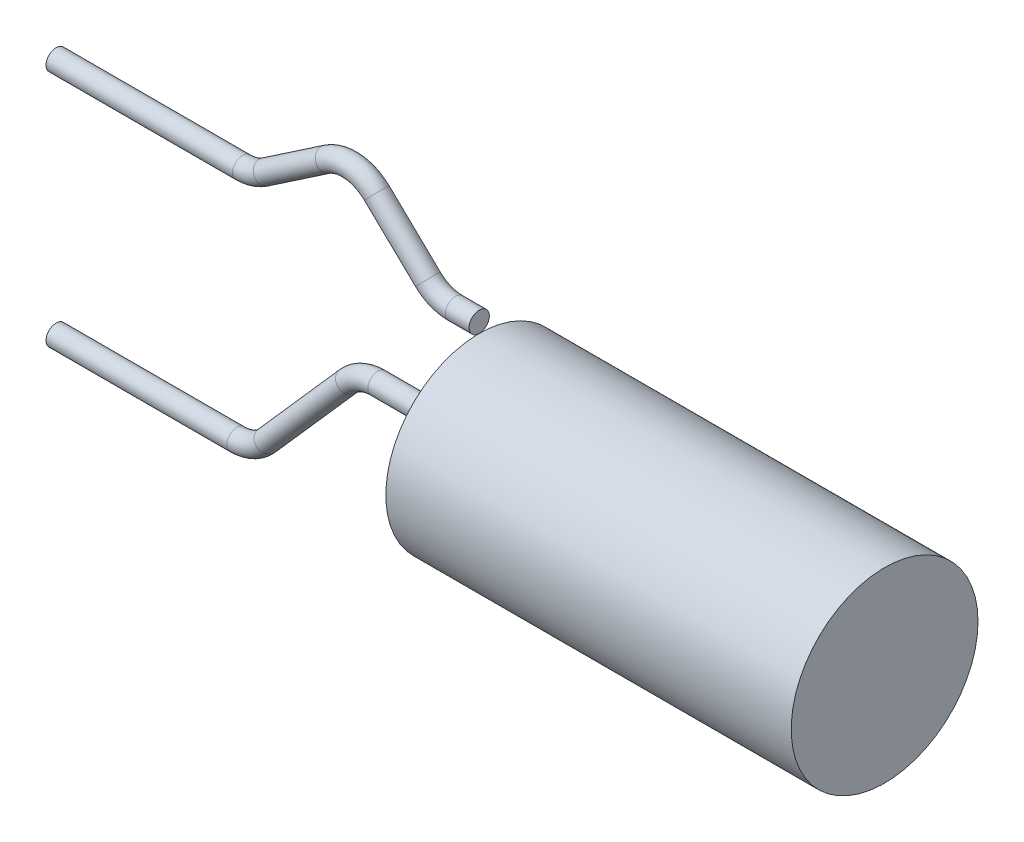
SolidWorks part; units mm, degrees
ref_plane "Plane1" through (0, 0, 0) normal (0, 0, 1) x (1, 0, 0)
ref_plane "Plane2" through (0, 0, 0) normal (0, 1, 0) x (1, 0, 0)
ref_plane "Plane3" through (0, 0, 0) normal (1, 0, 0) x (0, 0, -1)
sketch "Sketch1" plane through (0, 0, 0) normal (0, 0, 1) x (1, 0, 0)
  line L0 (0, 0) -> (-25.9084, 0) construction
  line L1 (-10.2, 0) -> (0, 0)
  line L2 (0, 0) -> (0, 2.35)
  line L3 (0, 2.35) -> (-10.2, 2.35)
  line L4 (-10.2, 0) -> (-10.2, 2.35)
  dimension "D1" = 10.2
  dimension "D2" = 4.7
revolve "Revolve1" add sketch "Sketch1" angle 360 about L0
sketch "Sketch4" plane through (0, 0, 0) normal (0, 0, 1) x (1, 0, 0)
  line L0 (-10.2, 0) -> (-12.7486, 0)
  line L1 (-10.2, 2.35) -> (-10.2, -2.35) construction
  line L2 (-13.4986, -0.3386) -> (-15.5472, -2.6614)
  line L3 (-16.2972, -3) -> (-20.8458, -3)
  line L5 (-15.8458, 3) -> (-13.3629, 4.6839) construction
  line L6 (-15.8458, 3) -> (-20.8458, 3) construction
  line L7 (0, 0) -> (-30.9014, 0) construction
  line L8 (-13.3629, 4.6839) -> (-11.2, 2.605) construction
  line L9 (0, 2.35) -> (-10.2, 2.35) construction
  line L10 (-11.2, 2.605) -> (-10.2, 2.605) construction
  arc A0 (-15.5472, -2.6614) -> (-16.2972, -3) centre (-16.2972, -2) cw
  arc A1 (-12.7486, 0) -> (-13.4986, -0.3386) centre (-12.7486, -1) ccw
  point P17 (-15.8458, -3)
  point P20 (-13.2, 0)
  dimension "D9" = 1
  dimension "D1" = 3
  dimension "D2" = 4
  dimension "D3" = 6
  dimension "D4" = 5
  dimension "D5" = 5
  dimension "D6" = 0.255
  dimension "D7" = 3
  dimension "D8" = 3
  dimension "D10" = 1
sketch "Sketch5" plane through (-10.2, 0, 0) normal (-1, 0, 0) x (0, 0, 1)
  circle A0 centre (0, 0) radius 0.255
  dimension "D1" = 0.51
sweep "Sweep1" add profiles "Sketch5" path "Sketch4"
sketch "Sketch6" plane through (0, 0, 0) normal (0, 0, 1) x (1, 0, 0)
  line L0 (-15.8458, 3) -> (-20.8458, 3) construction
  line L1 (-15.8458, 3) -> (-13.3629, 4.6839) construction
  line L2 (-13.3629, 4.6839) -> (-11.2, 2.605) construction
  line L3 (-11.2, 2.605) -> (-10.2, 2.605) construction
  line L4 (-16.1529, 3) -> (-20.8458, 3)
  line L5 (-15.5916, 3.1724) -> (-14.0332, 4.2293)
  line L6 (-12.779, 4.1226) -> (-11.4903, 2.884)
  line L7 (-10.7973, 2.605) -> (-10.2, 2.605)
  arc A0 (-16.1529, 3) -> (-15.5916, 3.1724) centre (-16.1529, 4) ccw
  arc A1 (-14.0332, 4.2293) -> (-12.779, 4.1226) centre (-13.4719, 3.4017) cw
  arc A2 (-11.4903, 2.884) -> (-10.7973, 2.605) centre (-10.7973, 3.605) ccw
  dimension "D1" = 1
sketch "Sketch7" plane through (-10.2, 0, 0) normal (-1, 0, 0) x (0, 0, 1)
  circle A0 centre (0, 2.605) radius 0.255
  circle A1 centre (0, 0) radius 0.255 construction
sweep "Sweep2" add profiles "Sketch7" path "Sketch6"
